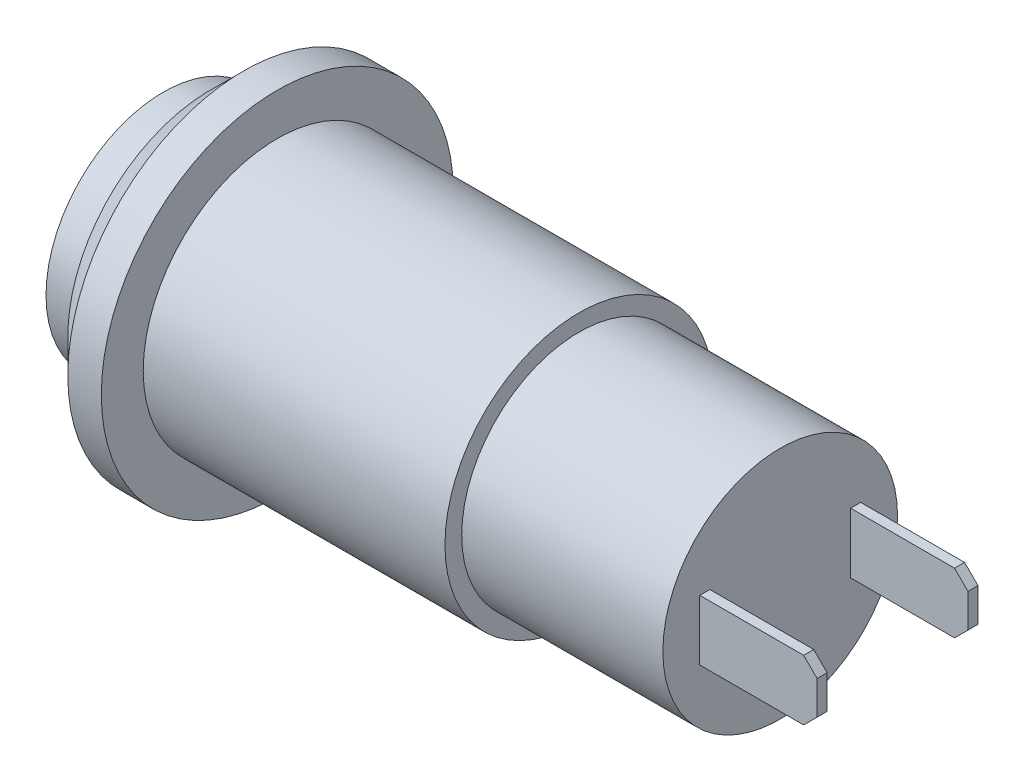
SolidWorks part; units mm, degrees
ref_plane "Front Plane" through (0, 0, 0) normal (0, 0, 1) x (1, 0, 0)
ref_plane "Top Plane" through (0, 0, 0) normal (0, 1, 0) x (1, 0, 0)
ref_plane "Right Plane" through (0, 0, 0) normal (1, 0, 0) x (0, 0, -1)
sketch "Sketch1" plane through (0, 0, 0) normal (0, 0, 1) x (1, 0, 0)
  line L0 (0, 0) -> (18.4, 0) construction
  line L1 (18.4, 0) -> (18.4, 3.5)
  line L2 (18.4, 3.5) -> (12.4, 3.5)
  line L3 (12.4, 3.5) -> (12.4, 4)
  line L4 (12.4, 4) -> (3.4, 4)
  line L5 (3.4, 4) -> (3.4, 5.25)
  line L6 (3.4, 5.25) -> (1.4, 5.25)
  line L7 (1.4, 5.25) -> (1.4, 3.5)
  line L8 (1.4, 3.5) -> (0, 3.5)
  line L9 (0, 3.5) -> (0, 0)
  line L10 (0, 0) -> (18.4, 0)
  point P3 (2.4, 5.25)
  dimension "D1" = 8
  dimension "D2" = 7
  dimension "D3" = 7
  dimension "D4" = 10.5
  dimension "D5" = 2
  dimension "D6" = 1.4
  dimension "D7" = 9
  dimension "D8" = 18.4
revolve "Revolve1" add sketch "Sketch1" angle 360 about L0
cosmetic thread "Cosmetic Thread1" parameters "D2"=6.647
chamfer "Chamfer1" distance 1 angle 45 1 edges at (1.4, 0, 5.25)
sketch "Sketch2" plane through (18.4, 0, 0) normal (1, 0, 0) x (0, 0, -1)
  line L0 (-2.25, 0) -> (2.25, 0) construction
  line L1 (0, 0) -> (0, 3.021) construction
  line L2 (-2.4, -0.9) -> (-2.1, -0.9)
  line L3 (-2.4, -0.9) -> (-2.4, 0.9)
  line L4 (-2.4, 0.9) -> (-2.1, 0.9)
  line L5 (-2.1, -0.9) -> (-2.1, 0.9)
  line L6 (-2.4, -0.9) -> (-2.1, 0.9) construction
  line L7 (-2.4, 0.9) -> (-2.1, -0.9) construction
  line L8 (2.1, -0.9) -> (2.4, -0.9)
  line L9 (2.1, -0.9) -> (2.1, 0.9)
  line L10 (2.1, 0.9) -> (2.4, 0.9)
  line L11 (2.4, -0.9) -> (2.4, 0.9)
  line L12 (2.1, -0.9) -> (2.4, 0.9) construction
  line L13 (2.1, 0.9) -> (2.4, -0.9) construction
  point P4 (0, 0)
  point P16 (0, 0)
  dimension "D1" = 1.8
  dimension "D2" = 0.3
  dimension "D3" = 4.8
extrude "Boss-Extrude1" add sketch "Sketch2" along normal blind 3.5
chamfer "Chamfer2" distance 0.4 angle 45 4 edges at (21.9, -0.9, -2.25) (21.9, 0.9, -2.25) (21.9, -0.9, 2.25) (21.9, 0.9, 2.25)
